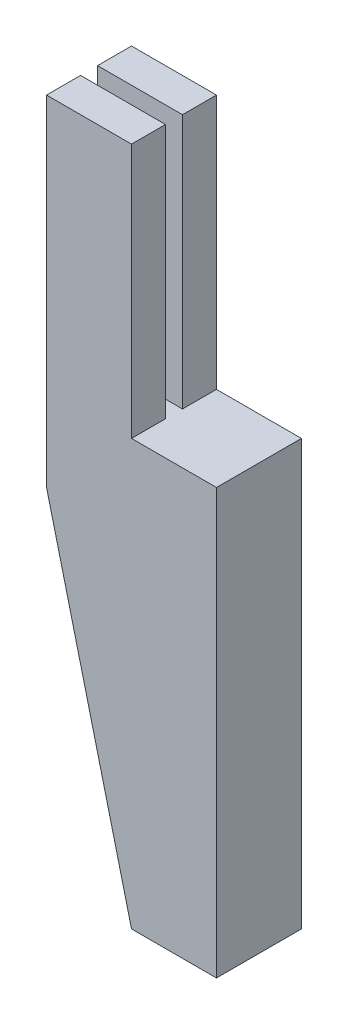
SolidWorks part; units mm, degrees
ref_plane "Ön Düzlem" through (0, 0, 0) normal (0, 0, 1) x (1, 0, 0)
ref_plane "Üst Düzlem" through (0, 0, 0) normal (0, 1, 0) x (1, 0, 0)
ref_plane "Sağ Düzlem" through (0, 0, 0) normal (1, 0, 0) x (0, 0, -1)
sketch "Sketch1" plane through (0, 0, 0) normal (0, 0, 1) x (1, 0, 0)
  line L0 (0, 0) -> (0, 30)
  line L1 (0, 30) -> (-10, 30)
  line L2 (-10, 30) -> (-10, -10)
  line L3 (-10, -10) -> (0, -50)
  line L4 (0, -50) -> (10, -50)
  line L5 (10, -50) -> (10, 0)
  line L6 (10, 0) -> (0, 0)
  dimension "D1" = 10
  dimension "D2" = 40
  dimension "D3" = 10
  dimension "D4" = 10
  dimension "D5" = 50
  dimension "D6" = 30
extrude "Boss-Extrude1" add sketch "Sketch1" along normal blind 10
sketch "Sketch2" plane through (0, 30, 0) normal (0, 1, 0) x (1, 0, 0)
  line L0 (-10, -10) -> (-10, 0) construction
  line L1 (-10, -4) -> (0, -4)
  line L2 (-10, -4) -> (-10, -6)
  line L3 (-10, -6) -> (0, -6)
  line L4 (0, -4) -> (0, -6)
  line L5 (0, -10) -> (0, 0) construction
  dimension "D1" = 2
  dimension "D2" = 4
extrude "Cut-Extrude1" cut sketch "Sketch2" against normal blind 30
